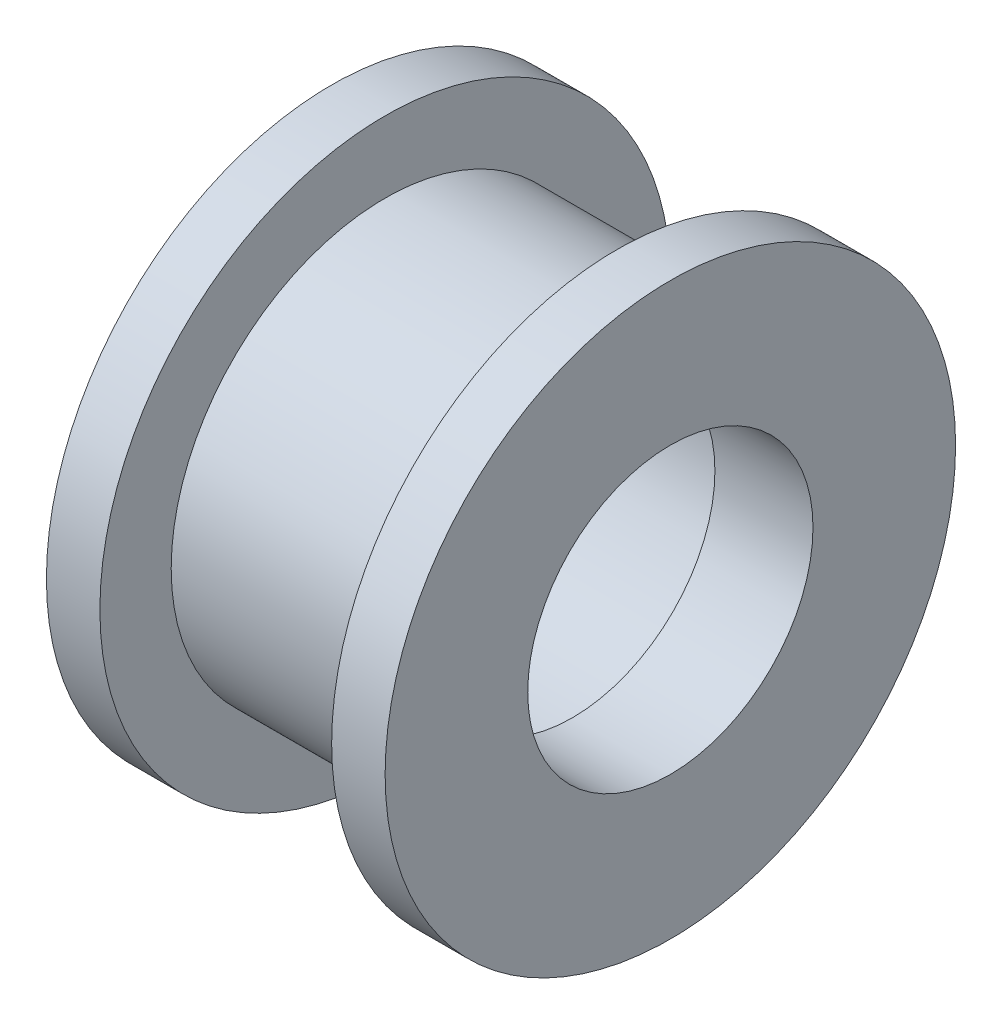
SolidWorks part; units mm, degrees
ref_plane "Plan de face" through (0, 0, 0) normal (0, 0, 1) x (1, 0, 0)
ref_plane "Plan de dessus" through (0, 0, 0) normal (0, 1, 0) x (1, 0, 0)
ref_plane "Plan de droite" through (0, 0, 0) normal (1, 0, 0) x (0, 0, -1)
sketch "Esquisse2" plane through (0, 0, 0) normal (0, 0, 1) x (1, 0, 0)
  line L0 (-5.5, 4.975) -> (1.25, 4.975)
  line L1 (4, 4) -> (4, 8)
  line L2 (4, 8) -> (2.5, 8)
  line L3 (2.5, 8) -> (2.5, 6)
  line L4 (2.5, 6) -> (-4, 6)
  line L5 (-4, 6) -> (-4, 8)
  line L6 (-4, 8) -> (-5.5, 8)
  line L7 (-5.5, 8) -> (-5.5, 4.975)
  line L8 (-17.3034, 0) -> (20.2621, 0) construction
  line L9 (-2.75, 6) -> (-2.75, 0) construction
  line L10 (4, 4) -> (1.25, 4)
  line L11 (1.25, 4) -> (1.25, 4.975)
  dimension "D1" = 9.95
  dimension "D2" = 6.5
  dimension "D3" = 1.5
  dimension "D4" = 1.5
  dimension "D5" = 2
  dimension "D6" = 2
  dimension "D7" = 6
  dimension "D8" = 5.5
  dimension "D9" = 4
  dimension "D10" = 4
  dimension "D11" = 1.25
revolve "Révolution1" add sketch "Esquisse2" angle 360 about L8
